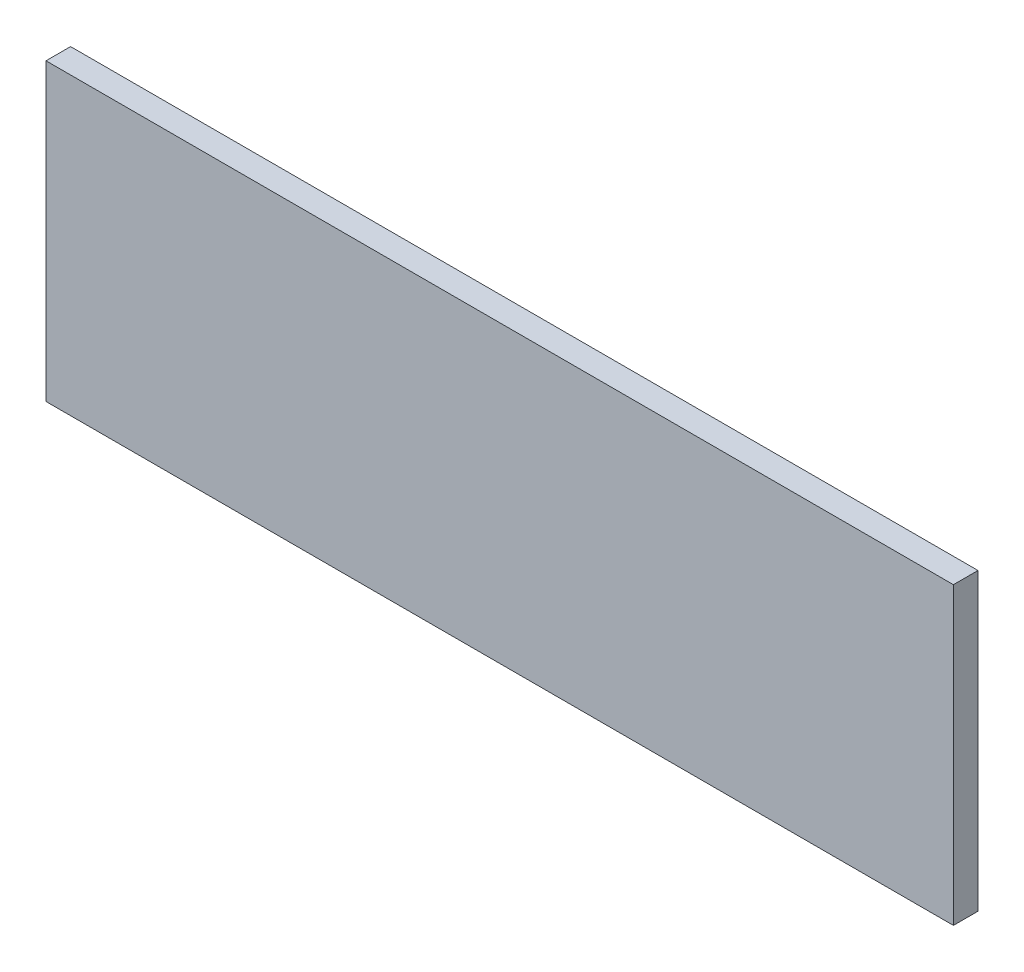
SolidWorks part; units mm, degrees
ref_plane "Front Plane" through (0, 0, 0) normal (0, 0, 1) x (1, 0, 0)
ref_plane "Top Plane" through (0, 0, 0) normal (0, 1, 0) x (1, 0, 0)
ref_plane "Right Plane" through (0, 0, 0) normal (1, 0, 0) x (0, 0, -1)
sketch "Sketch1" plane through (0, 0, 0) normal (0, 0, 1) x (1, 0, 0)
  line L1 (0, 0) -> (46.125, 0)
  line L2 (0, 0) -> (0, 15)
  line L3 (0, 15) -> (46.125, 15)
  line L4 (46.125, 0) -> (46.125, 15)
  dimension "D1" = 46.125
  dimension "D2" = 15
extrude "Boss-Extrude1" add sketch "Sketch1" along normal blind 1.25
